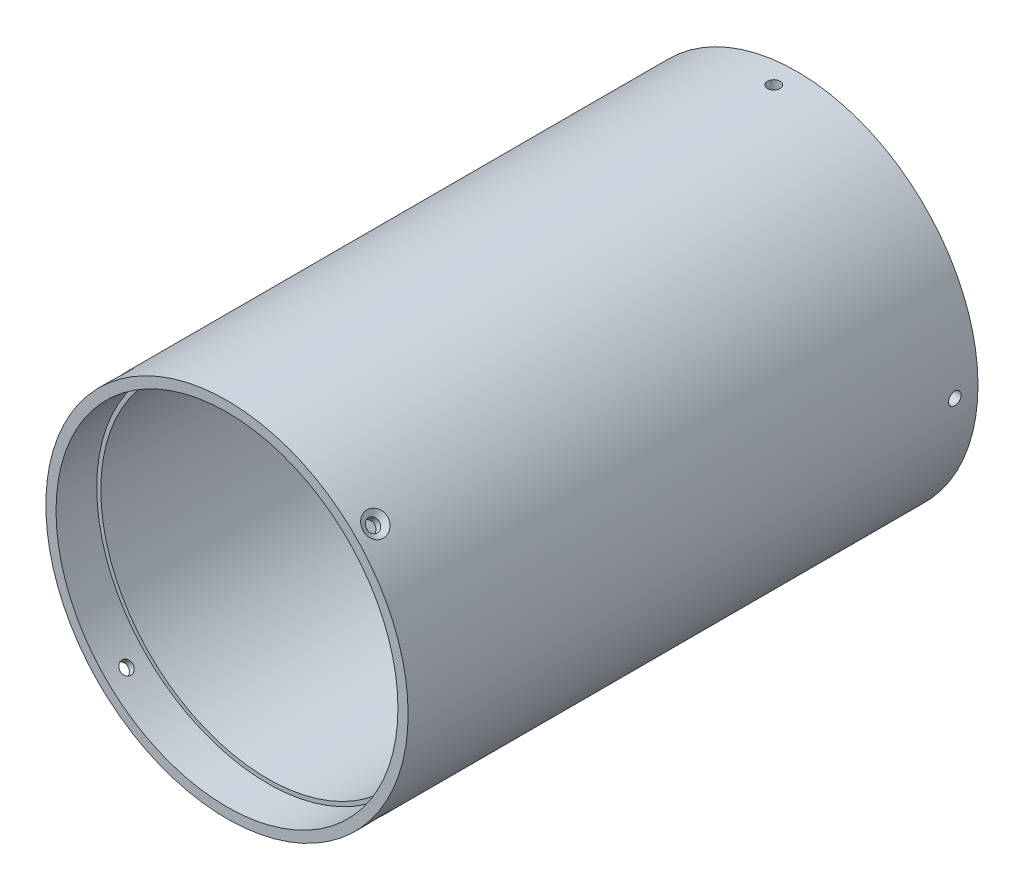
SolidWorks part; units mm, degrees
material "Hexcel AS4C (3000 Filaments)"
ref_plane "Plan de face" through (0, 0, 0) normal (0, 0, 1) x (1, 0, 0)
ref_plane "Plan de dessus" through (0, 0, 0) normal (0, 1, 0) x (1, 0, 0)
ref_plane "Plan de droite" through (0, 0, 0) normal (1, 0, 0) x (0, 0, -1)
sketch "Esquisse1" plane through (0, 0, 0) normal (0, 0, 1) x (1, 0, 0)
  circle A0 centre (0, 0) radius 44.5
  dimension "D1" = 89
extrude "Boss.-Extru.1" add sketch "Esquisse1" along normal blind 140
sketch "Esquisse2" plane through (0, 0, 0) normal (0, 0, -1) x (-1, 0, 0)
  circle A0 centre (0, 0) radius 42
  dimension "D1" = 84
extrude "Enlèv. mat.-Extru.1" cut sketch "Esquisse2" against normal blind 150
hole_wizard "Dégagement M2.51" positions "Esquisse3D1" profile "Esquisse5" hole size "M2.5" standard "ISO"
sketch3d "Esquisse3D1"
  line L7 (0, 0, 135) -> (-67.3052, 0, 135) construction
  line L8 (0, 0, 135) -> (-43.633, 43.633, 135) construction
  point P28 (-31.4663, 31.4663, 135)
  dimension "D1" = 135
  dimension "D2" = 45
sketch "Esquisse5" plane through (-31.4663, 31.4663, 135) normal (0, 0, 1) x (-0.7071, -0.7071, 0)
  line L0 (0, 0) -> (0, 15.9313)
  line L1 (0, 15.9313) -> (1.55, 15)
  line L2 (1.55, 15) -> (1.55, 0.8372)
  line L3 (1.55, 0.8372) -> (3, 0)
  line L5 (3, 0) -> (0, 0)
  line L6 (-1.55, 0.8372) -> (-3, 0) construction
  line L10 (0, 15.9313) -> (-1.55, 15) construction
  line L11 (0, -6.35) -> (0, 107.95) construction
  dimension "Diamètre du perçage" = 3.1
  dimension "Profondeur du perçage" = 15
  dimension "Diamètre du fraisage entrant" = 6
  dimension "Angle du fraisage entrant" = 120
  dimension "Angle de pointe" = 118
pattern_circular "Répétition circulaire1" count 4 every 90 about axis through (0, 0, 150) along (0, 0, -1) of "Dégagement M2.51"
sketch "Esquisse8" plane through (0, 0, 0) normal (0, 1, 0) x (1, 0, 0)
  line L0 (0, 17.4209) -> (0, -169.7882) construction
  line L1 (-41, 0) -> (-42, 0)
  line L2 (-42, 0) -> (-42, -130)
  line L3 (-42, -130) -> (-41, -130)
  line L4 (-41, -130) -> (-41, 0)
  point P5 (0, 0)
  dimension "D1" = 1
  dimension "D2" = 130
revolve "Révolution1" add sketch "Esquisse8" angle 360 about L0
hole_wizard "Dégagement M2.52" positions "Esquisse3D2" profile "Esquisse7" hole size "M2.5" standard "ISO"
sketch3d "Esquisse3D2"
  line L0 (0, 0, 0) -> (-75.2448, 0, 0) construction
  line L4 (-44.5, 0, 58.0044) -> (-44.5, 0, 0) construction
  circle A0 centre (0, 0, 0) radius 44.5 construction
  point P0 (-44.5, 0, 5.7)
  point P17 (0, 0, 44.5)
  dimension "D1" = 5.7
sketch "Esquisse7" plane through (-44.5, 0, 5.7) normal (0, 1, 0) x (0, 0, 1)
  line L0 (0, 0) -> (0, 20.9313)
  line L1 (0, 20.9313) -> (1.55, 20)
  line L2 (1.55, 20) -> (1.55, 0)
  line L5 (1.55, 0) -> (0, 0)
  line L10 (0, 20.9313) -> (-1.55, 20) construction
  line L11 (0, -6.35) -> (0, 107.95) construction
  dimension "Diamètre du perçage" = 3.1
  dimension "Profondeur du perçage" = 20
  dimension "Angle de pointe" = 118
pattern_circular "Répétition circulaire2" count 4 over 360 about axis through (0, 0, 0) along (0, 0, 1) of "Dégagement M2.52"
